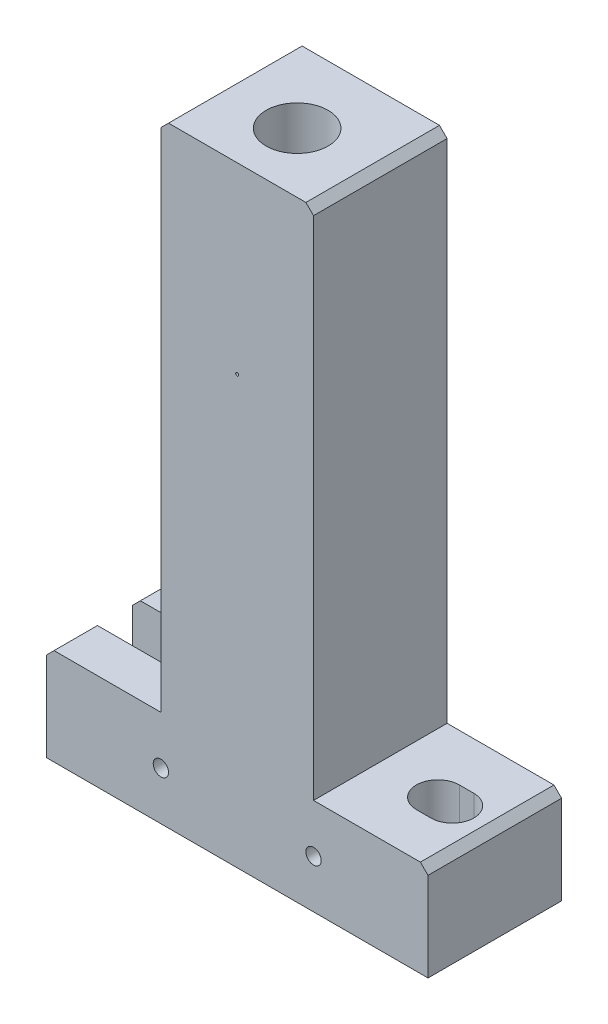
SolidWorks part; units mm, degrees
material "6061-T6 Al"
ref_plane "Front Plane" through (0, 0, 0) normal (0, 0, 1) x (1, 0, 0)
ref_plane "Top Plane" through (0, 0, 0) normal (0, 1, 0) x (1, 0, 0)
ref_plane "Right Plane" through (0, 0, 0) normal (1, 0, 0) x (0, 0, -1)
sketch "Sketch1" plane through (0, 0, 0) normal (0, 0, 1) x (1, 0, 0)
  line L0 (-63.5, 19.1623) -> (-25.4, 19.1623)
  line L1 (-63.5, 19.1623) -> (-63.5, -12.9687)
  line L2 (-63.5, -12.9687) -> (0, -12.9687)
  line L3 (0, -12.9687) -> (0, 190.2313)
  line L4 (0, 190.2313) -> (-25.4, 190.2313)
  line L5 (-25.4, 190.2313) -> (-25.4, 19.1623)
  dimension "D1" = 63.5
  dimension "D2" = 25.4
  dimension "D3" = 32.131
  dimension "D4" = 203.2
extrude "Extrude1" add sketch "Sketch1" along normal blind 44.45
mirror "Mirror2" about plane through (0, -12.9687, 44.45) normal (-1, 0, 0) of "Extrude1"
chamfer "Chamfer1" distance 2.54 angle 45 2 edges at (25.4, 190.2313, 22.225) (63.5, 19.1623, 22.225)
chamfer "Chamfer2" distance 2.54 angle 45 2 edges at (-63.5, 19.1623, 22.225) (-25.4, 190.2313, 22.225)
hole_wizard "13/16 (0.8125) Diameter Hole1" positions "3DSketch6" profile "Sketch13" hole size "13/16" standard "Ansi Inch"
sketch3d "3DSketch6"
  line L0 (22.86, 190.2313, 0) -> (-22.86, 190.2313, 0) construction
  line L2 (0, 190.2313, 24.511) -> (0, 190.2313, 0) construction
  point P0 (0, 190.2313, 24.511)
  dimension "D1" = 24.511
sketch "Sketch13" plane through (0, 190.2313, 24.511) normal (1, 0, 0) x (0, 0, 1)
  line L0 (0, 0) -> (0, 63.754)
  line L1 (0, 63.754) -> (10.3187, 63.754)
  line L2 (10.3187, 63.754) -> (10.3187, 0)
  line L5 (10.3187, 0) -> (0, 0)
  line L10 (0, 63.754) -> (-10.3188, 63.754) construction
  line L11 (0, -6.35) -> (0, 107.95) construction
  dimension "Hole Dia." = 20.6375
  dimension "Hole Depth" = 63.754
  dimension "Drill Angle" = 180
hole_wizard "1/2-20 Tapped Hole1" positions "3DSketch9" profile "Sketch16" tap size "1/2-20" standard "Ansi Inch"
sketch3d "3DSketch9"
  circle A0 centre (0, 126.4773, 24.511) radius 10.3187 construction
  point P0 (0, 126.4773, 24.511)
  point P5 (0, 136.7961, 24.511)
  dimension "D1" = 0
cosmetic thread "Hole Thread2" parameters "D1"=70.866, "D2"=12.7
sketch "Sketch16" plane through (0, 126.4773, 24.511) normal (1, 0, 0) x (0, 0, 1)
  line L0 (0, 0) -> (0, 85.8723)
  line L1 (0, 85.8723) -> (5.7544, 82.55)
  line L2 (5.7544, 82.55) -> (5.7544, 0)
  line L5 (5.7544, 0) -> (0, 0)
  line L10 (0, 85.8723) -> (-5.7544, 82.55) construction
  line L11 (0, -6.35) -> (0, 107.95) construction
  dimension "Tap Drill Dia." = 11.5087
  dimension "Tap Drill Depth" = 82.55
  dimension "Drill Angle" = 120
hole_wizard "#60 (0.04) Diameter Hole1" positions "Sketch18" profile "Sketch17" hole size "#60" standard "Ansi Inch"
sketch "Sketch18" plane through (0, 0, 44.45) normal (0, 0, 1) x (1, 0, 0)
  line L0 (-63.5, -12.9687) -> (63.5, -12.9687) construction
  line L1 (-25.4, 187.6913) -> (-25.4, 19.1623) construction
  point P0 (0, 129.2713)
  dimension "D1" = 142.24
  dimension "D2" = 25.4
sketch "Sketch17" plane through (0, 129.2713, 44.45) normal (1, 0, 0) x (0, -1, 0)
  line L0 (0, 0) -> (0, 9.6203)
  line L1 (0, 9.6203) -> (0.508, 9.6203)
  line L2 (0.508, 9.6203) -> (0.508, 0)
  line L5 (0.508, 0) -> (0, 0)
  line L11 (0, -6.35) -> (0, 107.95) construction
  dimension "Thru Hole Dia." = 1.016
  dimension "Thru Hole Depth" = 9.6203
hole_wizard "1/4-20 Tapped Hole1" positions "Sketch20" profile "Sketch19" tap size "1/4-20" standard "Ansi Inch" end condition through all
sketch "Sketch20" plane through (0, 0, 0) normal (0, 0, -1) x (-1, 0, 0)
  line L0 (63.5, -12.9687) -> (-63.5, -12.9687) construction
  line L2 (-63.5, 16.6223) -> (-63.5, -12.9687) construction
  line L3 (63.5, 16.6223) -> (63.5, -12.9687) construction
  point P0 (-25.4, 3.0968)
  point P1 (25.4, 3.0968)
  dimension "D1" = 16.0655
  dimension "D2" = 16.0655
  dimension "D3" = 38.1
  dimension "D4" = 38.1
sketch "Sketch19" plane through (25.4, 3.0968, 0) normal (1, 0, 0) x (0, 1, 0)
  line L0 (0, 0) -> (0, 44.45)
  line L1 (0, 44.45) -> (2.5527, 44.45)
  line L2 (2.5527, 44.45) -> (2.5527, 0)
  line L5 (2.5527, 0) -> (0, 0)
  line L11 (0, -6.35) -> (0, 107.95) construction
  dimension "Thru Tap Drill Dia." = 5.1054
  dimension "Thru Tap Drill Depth" = 44.45
cosmetic thread "Hole Thread3" parameters "D2"=6.35
cosmetic thread "Hole Thread4" parameters "D2"=6.35
hole_wizard "1/4 (0.25) Diameter Hole2" positions "Sketch22" profile "Sketch21" hole size "1/4" standard "Ansi Inch"
sketch "Sketch22" plane through (0, 0, 0) normal (0, 0, -1) x (-1, 0, 0)
  line L0 (63.5, -12.9687) -> (-63.5, -12.9687) construction
  line L1 (-63.5, 16.6223) -> (-63.5, -12.9687) construction
  point P0 (-9.525, 3.0968)
  dimension "D1" = 16.0655
  dimension "D2" = 53.975
sketch "Sketch21" plane through (9.525, 3.0968, 0) normal (1, 0, 0) x (0, 1, 0)
  line L0 (0, 0) -> (0, 14.6131)
  line L1 (0, 14.6131) -> (3.1839, 12.7)
  line L2 (3.1839, 12.7) -> (3.1839, 1.6421)
  line L3 (3.1839, 1.6421) -> (4.826, 0)
  line L5 (4.826, 0) -> (0, 0)
  line L6 (-3.1839, 1.6421) -> (-4.826, 0) construction
  line L10 (0, 14.6131) -> (-3.1839, 12.7) construction
  line L11 (0, -6.35) -> (0, 107.95) construction
  dimension "Hole Dia." = 6.3678
  dimension "Hole Depth" = 12.7
  dimension "Near C'Sink Dia." = 9.652
  dimension "Near C'Sink Angle" = 90
  dimension "Drill Angle" = 118
sketch "Sketch23" plane through (0, 0, 0) normal (0, 0, -1) x (-1, 0, 0)
  line L0 (6.35, 3.0968) -> (12.7, 3.0968) construction
  line L1 (6.35, 6.2807) -> (12.7, 6.2807)
  line L2 (6.35, -0.087) -> (12.7, -0.087)
  line L3 (63.5, -12.9687) -> (-63.5, -12.9687) construction
  line L4 (-63.5, 16.6223) -> (-63.5, -12.9687) construction
  arc A0 (6.35, 6.2807) -> (6.35, -0.087) centre (6.35, 3.0968) ccw
  arc A1 (12.7, -0.087) -> (12.7, 6.2807) centre (12.7, 3.0968) ccw
  circle A2 centre (-9.525, 3.0968) radius 3.1839 construction
  point P2 (9.525, 3.0968)
  dimension "D4" = 69.85
  dimension "D2" = 16.0655
  dimension "D3" = 6.35
extrude "Extrude4" cut sketch "Sketch23" against normal blind 12.7
chamfer "Chamfer3" distance 1.524 angle 45 4 edges at (-15.8839, 3.0968, 0) (-9.525, 6.2807, 0) (-9.525, -0.087, 0) (-3.1661, 3.0968, 0)
sketch "Sketch24" plane through (0, 19.1623, 0) normal (0, 1, 0) x (1, 0, 0)
  line L0 (45.1834, -22.86) -> (50.0094, -22.86) construction
  line L1 (45.1834, -15.7226) -> (50.0094, -15.7226)
  line L2 (45.1834, -29.9974) -> (50.0094, -29.9974)
  line L3 (-38.2556, -22.86) -> (-63.6556, -22.86) construction
  line L4 (-38.2556, -29.9974) -> (-63.6556, -29.9974)
  line L5 (-38.2556, -15.7226) -> (-63.6556, -15.7226)
  line L6 (-38.2556, -22.86) -> (45.1834, -22.86) construction
  line L7 (-63.5, -44.45) -> (63.5, -44.45) construction
  arc A0 (45.1834, -15.7226) -> (45.1834, -29.9974) centre (45.1834, -22.86) ccw
  arc A1 (50.0094, -29.9974) -> (50.0094, -15.7226) centre (50.0094, -22.86) ccw
  arc A2 (-38.2556, -29.9974) -> (-38.2556, -15.7226) centre (-38.2556, -22.86) ccw
  arc A3 (-63.6556, -15.7226) -> (-63.6556, -29.9974) centre (-63.6556, -22.86) ccw
  circle A4 centre (0, -24.511) radius 5.7544 construction
  point P2 (47.5964, -22.86)
  point P7 (-50.9556, -22.86)
  dimension "D3" = 7.1374
  dimension "D1" = 47.625
  dimension "D2" = 4.826
  dimension "D4" = 85.852
  dimension "D5" = 25.4
  dimension "D6" = 21.59
extrude "Extrude5" cut sketch "Sketch24" against normal through all
